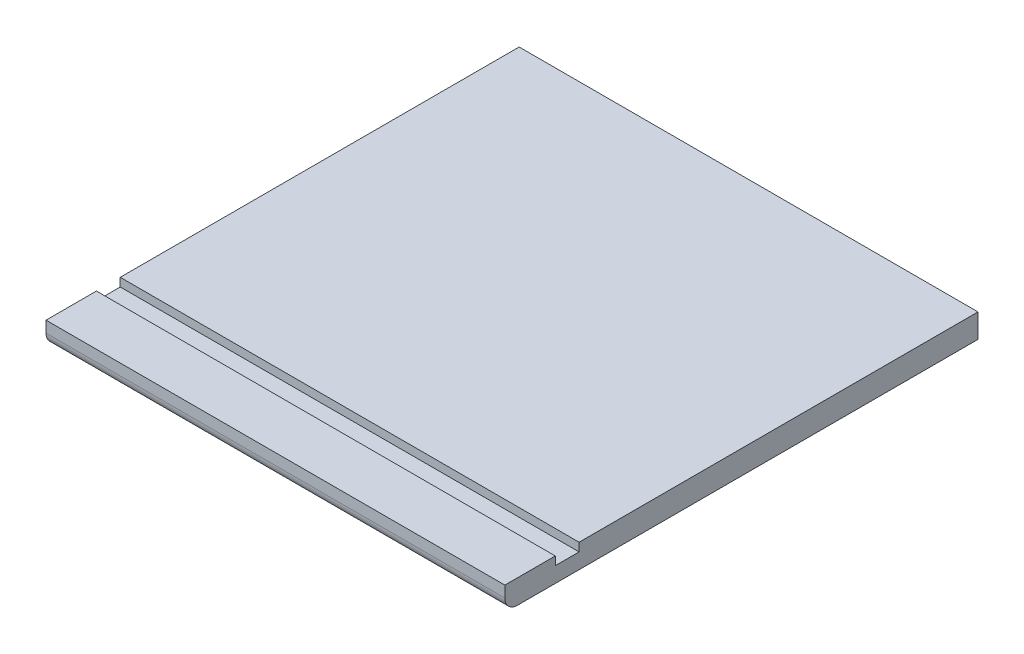
SolidWorks part; units mm, degrees
ref_plane "Front Plane" through (0, 0, 0) normal (0, 0, 1) x (1, 0, 0)
ref_plane "Top Plane" through (0, 0, 0) normal (0, 1, 0) x (1, 0, 0)
ref_plane "Right Plane" through (0, 0, 0) normal (1, 0, 0) x (0, 0, -1)
sketch "Sketch1" plane through (0, 0, 0) normal (0, 1, 0) x (1, 0, 0)
  line L1 (0, 0) -> (346.7, 0)
  line L2 (0, 0) -> (0, -357.5)
  line L3 (0, -357.5) -> (346.7, -357.5)
  line L4 (346.7, 0) -> (346.7, -357.5)
  dimension "D1" = 346.7
  dimension "D2" = 357.5
extrude "Boss-Extrude1" add sketch "Sketch1" along normal blind 18
sketch "Sketch2" plane through (0, 18, 0) normal (0, 1, 0) x (1, 0, 0)
  line L0 (0, -357.5) -> (346.7, -357.5) construction
  line L1 (346.7, -319.4) -> (0, -319.4)
  line L2 (346.7, -319.4) -> (346.7, -301.4)
  line L3 (346.7, -301.4) -> (0, -301.4)
  line L4 (0, -319.4) -> (0, -301.4)
  line L5 (0, 0) -> (0, -357.5) construction
  line L6 (346.7, -357.5) -> (346.7, 0) construction
  dimension "D1" = 18
  dimension "D2" = 38.1
  dimension "D3" = 0
  dimension "D4" = 0
extrude "Cut-Extrude1" cut sketch "Sketch2" against normal blind 6.35
fillet "Fillet1" radius 9.525 1 edges at (173.35, 0, 357.5)
